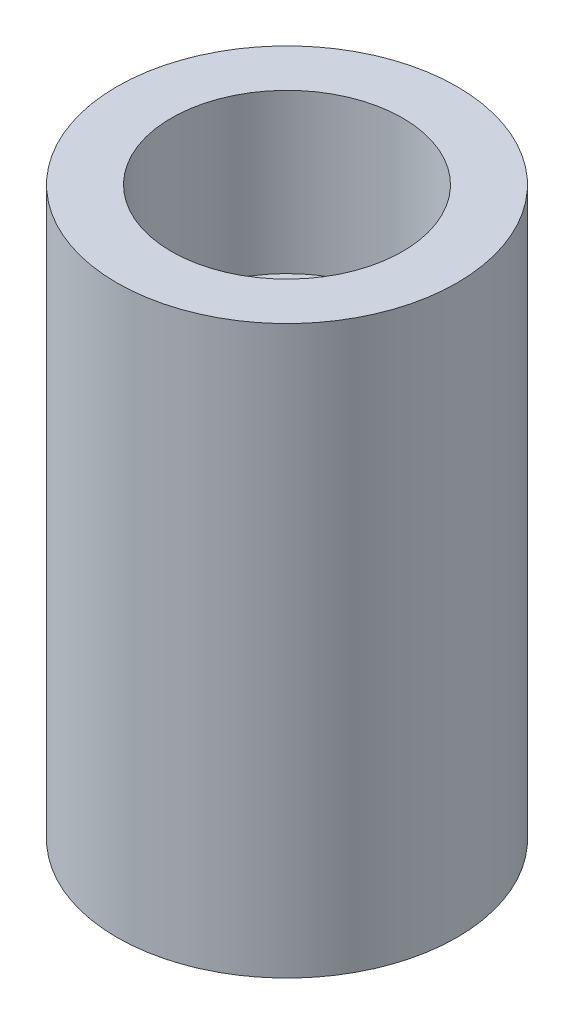
SolidWorks part; units mm, degrees
ref_plane "Front Plane" through (0, 0, 0) normal (0, 0, 1) x (1, 0, 0)
ref_plane "Top Plane" through (0, 0, 0) normal (0, 1, 0) x (1, 0, 0)
ref_plane "Right Plane" through (0, 0, 0) normal (1, 0, 0) x (0, 0, -1)
sketch "Sketch1" plane through (0, 0, 0) normal (0, 1, 0) x (1, 0, 0)
  circle A0 centre (0, 0) radius 7.5
  dimension "D1" = 15
extrude "Boss-Extrude1" add sketch "Sketch1" along normal blind 25
sketch "Sketch2" plane through (0, 0, 0) normal (0, -1, 0) x (1, 0, 0)
  circle A0 centre (0, 0) radius 5.1
  dimension "D1" = 10.2
extrude "Cut-Extrude1" cut sketch "Sketch2" against normal blind 7
sketch "Sketch3" plane through (0, 25, 0) normal (0, 1, 0) x (1, 0, 0)
  circle A0 centre (0, 0) radius 5.1
  dimension "D1" = 10.2
extrude "Cut-Extrude2" cut sketch "Sketch3" against normal blind 7
sketch "Sketch4" plane through (0, 18, 0) normal (0, 1, 0) x (1, 0, 0)
  circle A0 centre (0, 0) radius 4
  dimension "D1" = 8
extrude "Cut-Extrude3" cut sketch "Sketch4" against normal through all
